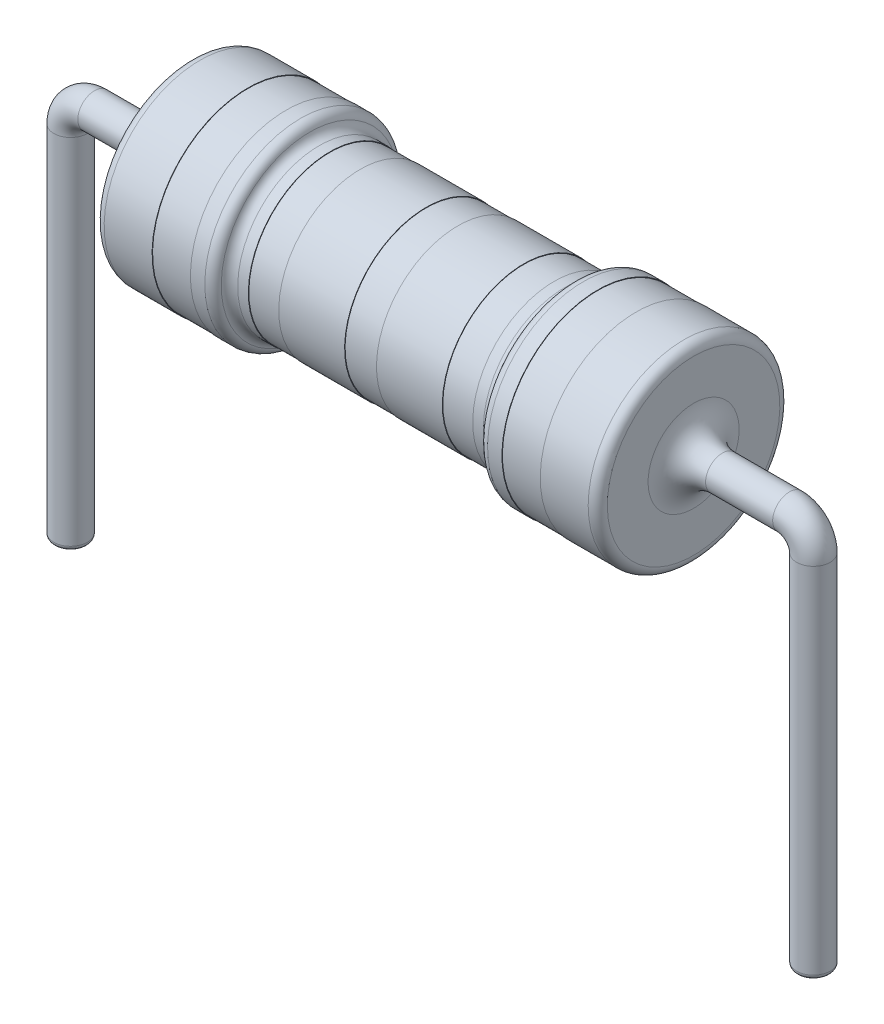
SolidWorks part; units mm, degrees
ref_plane "Front Plane" through (0, 0, 0) normal (0, 0, 1) x (1, 0, 0)
ref_plane "Top Plane" through (0, 0, 0) normal (0, 1, 0) x (1, 0, 0)
ref_plane "Right Plane" through (0, 0, 0) normal (1, 0, 0) x (0, 0, -1)
sketch "Sketch1" plane through (0, 0, 0) normal (0, 0, 1) x (1, 0, 0)
  line L0 (-5.25, 0) -> (5.25, 0)
  line L1 (5.25, 0) -> (5.25, -2)
  line L2 (5.25, -2) -> (4.05, -2)
  line L4 (4.05, -2) -> (4.05, -1.99)
  line L5 (4.05, -1.99) -> (3.25, -1.99)
  line L6 (3.25, -1.99) -> (3.25, -2)
  line L7 (3.25, -2) -> (2.75, -2)
  line L8 (2.75, -2) -> (2.75, -1.7)
  line L9 (2.75, -1.7) -> (2.3407, -1.7)
  line L10 (2.3407, -1.7) -> (2.3407, -1.69)
  line L11 (2.3407, -1.69) -> (1.7068, -1.69)
  line L12 (1.7068, -1.69) -> (1.7068, -1.7)
  line L13 (1.7068, -1.7) -> (0.3325, -1.7)
  line L14 (0.3325, -1.7) -> (0.3325, -1.69)
  line L15 (0.3325, -1.69) -> (-0.3325, -1.69)
  line L16 (-0.3325, -1.7) -> (-0.3325, -1.69)
  line L17 (-1.7068, -1.7) -> (-0.3325, -1.7)
  line L18 (-1.7068, -1.69) -> (-1.7068, -1.7)
  line L19 (-2.3407, -1.69) -> (-1.7068, -1.69)
  line L20 (-2.3407, -1.7) -> (-2.3407, -1.69)
  line L21 (-2.75, -1.7) -> (-2.3407, -1.7)
  line L22 (-2.75, -2) -> (-2.75, -1.7)
  line L23 (-3.25, -2) -> (-2.75, -2)
  line L24 (-3.25, -1.99) -> (-3.25, -2)
  line L25 (-4.05, -1.99) -> (-3.25, -1.99)
  line L26 (-4.05, -2) -> (-4.05, -1.99)
  line L27 (-5.25, -2) -> (-4.05, -2)
  line L28 (-5.25, 0) -> (-5.25, -2)
  point P20 (0, -1.69)
  point P33 (0, 0)
  dimension "D2" = 2.5
  dimension "D3" = 0.8
  dimension "D4" = 1.2
  dimension "D5" = 0.3
  dimension "D6" = 0.01
  dimension "D7" = 0.01
  dimension "D8" = 0.01
revolve "Revolve1" add sketch "Sketch1" angle 360 about L0
sketch "Sketch2" plane through (5.25, 0, 0) normal (1, 0, 0) x (0, 0, -1)
  circle A0 centre (0, 0) radius 0.4
fillet "Fillet2" radius 0.2 1 edges at (-2.75, -2, 0)
fillet "Fillet3" radius 0.2 2 edges at (-2.75, -1.7, 0) (2.75, -2, 0)
fillet "Fillet4" radius 0.2 1 edges at (2.75, -1.7, 0)
fillet "Fillet5" radius 0.2 1 edges at (-5.25, -2, 0)
fillet "Fillet6" radius 0.2 1 edges at (5.25, -2, 0)
ref_plane "Plane2" [suppressed] through (5.25, 0, 0) normal (1, 0, 0) x (0, 0, -1)
sketch3d "3DSketch7" [suppressed]
  line L0 (5.25, 0, 0) -> (7.75, 0, 0)
  line L1 (8.75, -1, 0) -> (8.75, -6, 0)
  arc A0 (7.75, 0, 0) -> (8.75, -1, 0) centre (7.75, -1, 0) ccw
  point P6 (8.75, 0, 0)
  point P7 (7.75, -1, -1)
  dimension "D3" = 1
  dimension "D1" = 3.5
  dimension "D2" = 6
sweep "Sweep3" [suppressed] add profiles "Sketch2" path "3DSketch7"
mirror "Mirror3" [suppressed] about plane through (0, 0, 0) normal (1, 0, 0)
fillet "Fillet12" [suppressed] radius 0.1
fillet "Fillet13" [suppressed] radius 0.8
fillet "Fillet14" [suppressed] radius 0.8
sketch "Sketch3" plane through (5.25, 0, 0) normal (1, 0, 0) x (0, 0, -1)
  circle A0 centre (0, 0) radius 0.35
sketch3d "3DSketch8"
  line L0 (5.25, 0, 0) -> (7.25, 0, 0)
  line L1 (7.75, -0.5, 0) -> (7.75, -7.9872, 0)
  arc A0 (7.75, -0.5, 0) -> (7.25, 0, 0) centre (7.25, -0.5, 0) ccw
  point P6 (7.75, 0, 0)
  point P7 (7.25, -0.5, 0.5)
  dimension "D2" = 0.5
  dimension "D1" = 2.5
sweep "Sweep4" add profiles "Sketch3" path "3DSketch8"
mirror "Mirror4" about plane through (0, 0, 0) normal (1, 0, 0) of "Sweep4"
fillet "Fillet15" radius 0.1 2 edges at (8.1, -7.9872, 0) (-8.1, -7.9872, 0)
fillet "Fillet16" radius 0.6 2 edges at (5.25, 0.35, 0) (-5.25, -0.35, 0)
